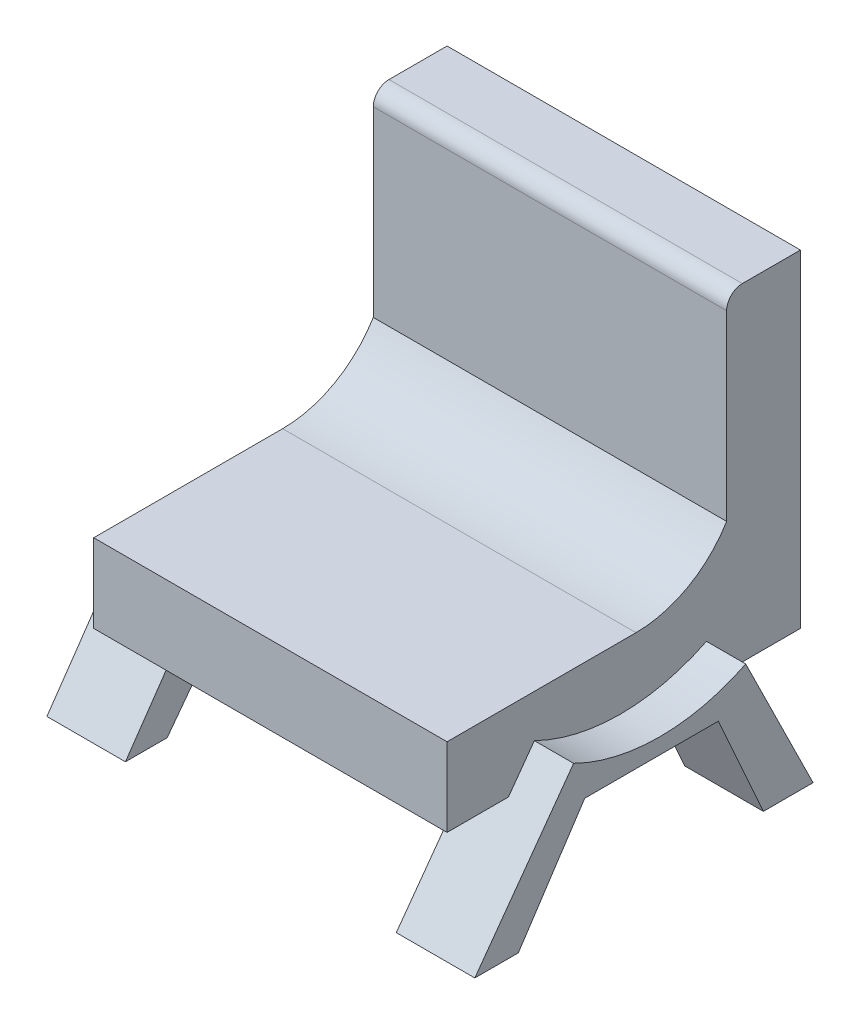
SolidWorks part; units mm, degrees
ref_plane "Front Plane" through (0, 0, 0) normal (0, 0, 1) x (1, 0, 0)
ref_plane "Top Plane" through (0, 0, 0) normal (0, 1, 0) x (1, 0, 0)
ref_plane "Right Plane" through (0, 0, 0) normal (1, 0, 0) x (0, 0, -1)
sketch "Sketch1" plane through (0, 0, 0) normal (1, 0, 0) x (0, 0, -1)
  line L0 (-48.1188, 0) -> (41.8812, 0)
  line L1 (-48.1188, 0) -> (-48.1188, 20)
  line L2 (-48.1188, 20) -> (0, 20)
  line L5 (41.8812, 83.467) -> (41.8812, 0)
  line L6 (23.0862, 32.999) -> (23.0862, 79.467)
  line L7 (27.0862, 83.467) -> (41.8812, 83.467)
  arc A0 (0, 20) -> (23.0862, 32.999) centre (0, 47) ccw
  arc A2 (23.0862, 79.467) -> (27.0862, 83.467) centre (27.0862, 79.467) cw
  point P7 (0, 0)
  point P11 (0, 0)
  point P12 (0, 0)
  dimension "D3" = 27
  dimension "D4" = 4
  dimension "D1" = 90
  dimension "D2" = 20
extrude "Boss-Extrude2" add sketch "Sketch1" against normal blind 90
sketch "Sketch2" plane through (0, 0, 0) normal (1, 0, 0) x (0, 0, -1)
  line L1 (-48.1188, 0) -> (41.8812, 0) construction
  line L2 (-32.4871, 0) -> (-51.0539, -25.6433)
  line L3 (-32.4871, 0) -> (-25.8836, 9.1204)
  line L4 (17.9479, 9.1204) -> (22.4485, 0)
  line L5 (22.4485, 0) -> (35.1023, -25.6433)
  line L6 (35.1023, -25.6433) -> (22.4485, -25.6433)
  line L7 (22.4485, -25.6433) -> (10.9569, 0)
  line L8 (10.9569, 0) -> (-23.0652, 0)
  line L9 (-23.0652, 0) -> (-39.9693, -25.6433)
  line L10 (-39.9693, -25.6433) -> (-51.0539, -25.6433)
  arc A0 (-25.8836, 9.1204) -> (17.9479, 9.1204) centre (-3.9678, 53.5331) ccw
  point P6 (0, 0)
extrude "Boss-Extrude4" add sketch "Sketch2" against normal mid plane 20
sketch "Sketch5" plane through (-90, 0, 0) normal (-1, 0, 0) x (0, 0, 1)
  line L0 (-15.0603, 7.3994) -> (28.775, 7.3994)
  line L1 (28.775, 7.3994) -> (50.0374, -23.4672)
  line L2 (50.0374, -23.4672) -> (39.4062, -23.4672)
  line L3 (39.4062, -23.4672) -> (21.794, 0)
  line L4 (48.1188, 0) -> (-41.8812, 0) construction
  line L5 (21.794, 0) -> (-13.2379, 0)
  line L6 (-13.2379, 0) -> (-23.1645, -23.4672)
  line L7 (-23.1645, -23.4672) -> (-36.5841, -23.4672)
  line L8 (-36.5841, -23.4672) -> (-21.2025, 7.3994)
  line L9 (-21.2025, 7.3994) -> (-15.0603, 7.3994)
extrude "Boss-Extrude5" add sketch "Sketch5" along normal mid plane 20
fillet "Fillet1" radius 10 2 edges at (-95, 7.3994, -21.2025) (-95, 7.3994, 28.775)
